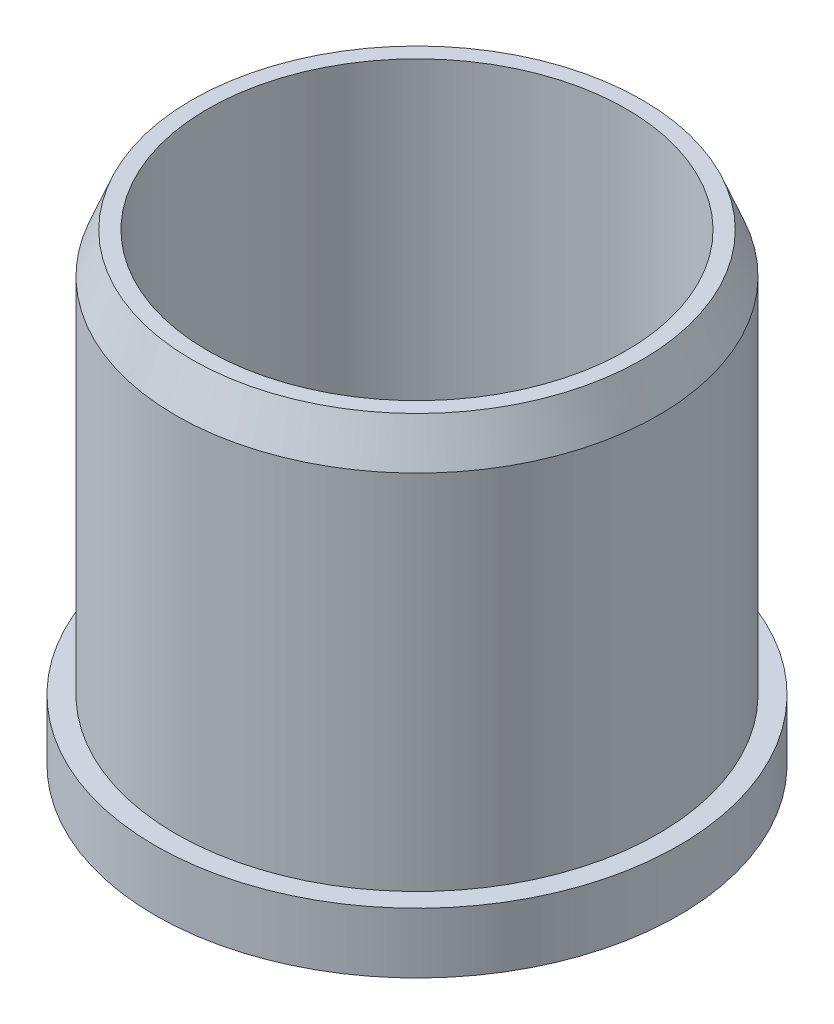
SolidWorks part; units mm, degrees
material "ABS"
ref_plane "Front Plane" through (0, 0, 0) normal (0, 0, 1) x (1, 0, 0)
ref_plane "Top Plane" through (0, 0, 0) normal (0, 1, 0) x (1, 0, 0)
ref_plane "Right Plane" through (0, 0, 0) normal (1, 0, 0) x (0, 0, -1)
sketch "Sketch1" plane through (0, 0, 0) normal (0, 1, 0) x (1, 0, 0)
  line L0 (0, 0) -> (7.1, 0)
  line L1 (7.1, 0) -> (9.6, 0)
  line L2 (9.6, 0) -> (9.6, 2.5)
  line L3 (9.6, 2.5) -> (6.6453, 2.5)
  line L4 (9.6, 0) -> (9.6, -2.5)
  line L5 (9.6, -2.5) -> (6.6453, -2.5)
  line L6 (0, 12.7) -> (0, 33.02)
  circle A0 centre (0, 0) radius 41.275
  circle A1 centre (0, 0) radius 7.1
  circle A2 centre (0, 0) radius 12.7
  circle A3 centre (0, 0) radius 33.02
  circle A4 centre (0, 22.86) radius 7.62
  circle A5 centre (21.7412, 7.0641) radius 7.62
  circle A6 centre (13.4368, -18.4941) radius 7.62
  circle A7 centre (-13.4368, -18.4941) radius 7.62
  circle A8 centre (-21.7412, 7.0641) radius 7.62
  point P26 (0, 0)
  dimension "D1" = 82.55
  dimension "D2" = 14.2
  dimension "D6" = 25.4
  dimension "D7" = 66.04
  dimension "D8" = 15.24
  dimension "D3" = 2.5
  dimension "D4" = 2.5
  dimension "D5" = 2.5
  dimension "D9" = 5
extrude "Boss-Extrude1" add sketch "Sketch1" along normal blind 9.525
sketch "Sketch2" plane through (0, 9.525, 0) normal (0, 1, 0) x (1, 0, 0)
  circle A0 centre (0, 0) radius 38.0365
  circle A1 centre (0, 0) radius 33.02
  dimension "D1" = 76.073
  dimension "D2" = 66.04
extrude "Boss-Extrude2" add sketch "Sketch2" along normal blind 63.5
sketch "Sketch3" plane through (0, 9.525, 0) normal (0, 1, 0) x (1, 0, 0)
  line L0 (6.6453, 2.5) -> (9.6, 2.5)
  line L1 (9.6, 2.5) -> (9.6, -2.5)
  line L2 (9.6, -2.5) -> (6.6453, -2.5)
  circle A0 centre (0, 0) radius 12.7
  circle A2 centre (0, 0) radius 7.1
  arc M5 (6.6453, -2.5) -> (6.6453, 2.5) centre (0, 0) cw
  line M6 (6.6453, 2.5) -> (9.6, 2.5)
  line M7 (9.6, 2.5) -> (9.6, -2.5)
  line M8 (9.6, -2.5) -> (6.6453, -2.5)
  dimension "D1" = 25.4
  dimension "D2" = 14.2
extrude "Boss-Extrude3" add sketch "Sketch3" along normal blind 15.875 contours A0 M8 M5 M6 M7
chamfer "Chamfer1" distance 6.35 distance2 2.54 1 edges at (0, 73.025, 38.0365)
sketch "Sketch4" plane through (0, 25.4, 0) normal (0, 1, 0) x (1, 0, 0)
  circle A0 centre (0, 0) radius 12.7
  dimension "D1" = 25.4
extrude "Boss-Extrude4" add sketch "Sketch4" along normal blind 6.35
fillet "Fillet1" radius 2.54 1 edges at (0, 31.75, 12.7)
